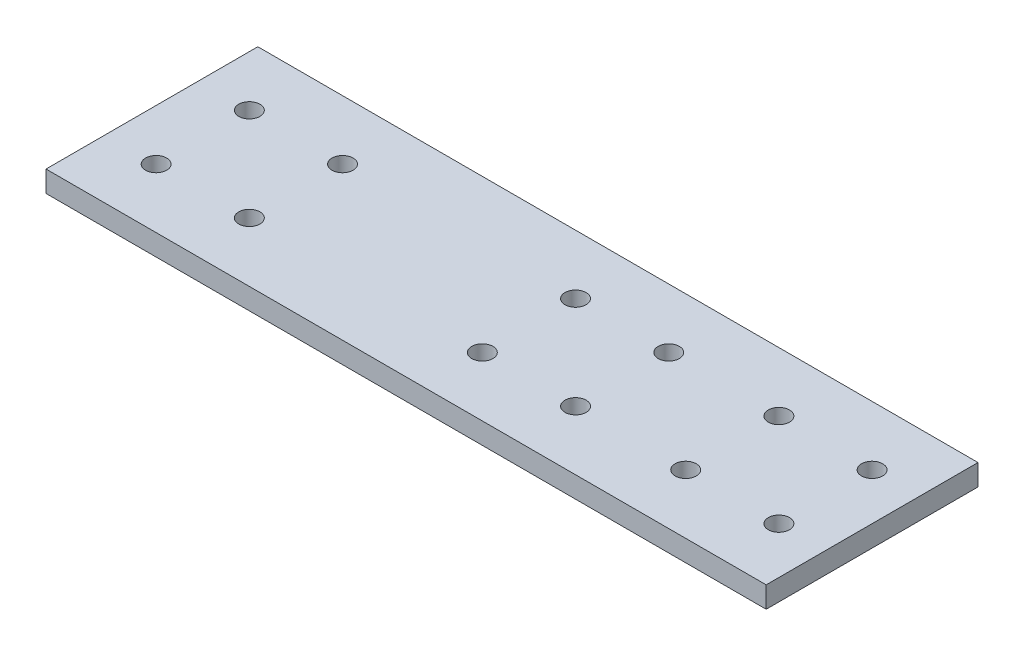
SolidWorks part; units mm, degrees
ref_plane "Piano frontale" through (0, 0, 0) normal (0, 0, 1) x (1, 0, 0)
ref_plane "Piano superiore" through (0, 0, 0) normal (0, 1, 0) x (1, 0, 0)
ref_plane "Piano destro" through (0, 0, 0) normal (1, 0, 0) x (0, 0, -1)
sketch "Sketch1" plane through (0, 0, 0) normal (0, 1, 0) x (1, 0, 0)
  line L0 (-85, 25) -> (85, -25) construction
  line L1 (-85, 25) -> (85, 25)
  line L2 (-85, 25) -> (-85, -25)
  line L3 (-85, -25) -> (85, -25)
  line L4 (85, 25) -> (85, -25)
  line L5 (-85, -25) -> (85, 25) construction
  line L16 (-85, 0) -> (85, 0) construction
  line L29 (-85, 11) -> (85, 11) construction
  circle A0 centre (74, 11) radius 2.5
  circle A1 centre (52, 11) radius 2.5
  circle A2 centre (52, -11) radius 2.5
  circle A3 centre (74, -11) radius 2.5
  circle A4 centre (26, 11) radius 2.5
  circle A5 centre (4, 11) radius 2.5
  circle A6 centre (4, -11) radius 2.5
  circle A7 centre (26, -11) radius 2.5
  circle A8 centre (-51, 11) radius 2.5
  circle A9 centre (-73, 11) radius 2.5
  circle A10 centre (-51, -11) radius 2.5
  circle A11 centre (-73, -11) radius 2.5
  point P4 (0, 0)
  dimension "D6" = 5
  dimension "D7" = 22
  dimension "D8" = 26
  dimension "D1" = 170
  dimension "D2" = 50
  dimension "D3" = 11
  dimension "D4" = 11
  dimension "D5" = 22
  dimension "D9" = 22
  dimension "D10" = 55
  dimension "D11" = 22
extrude "Boss-Extrude1" add sketch "Sketch1" along normal blind 5
